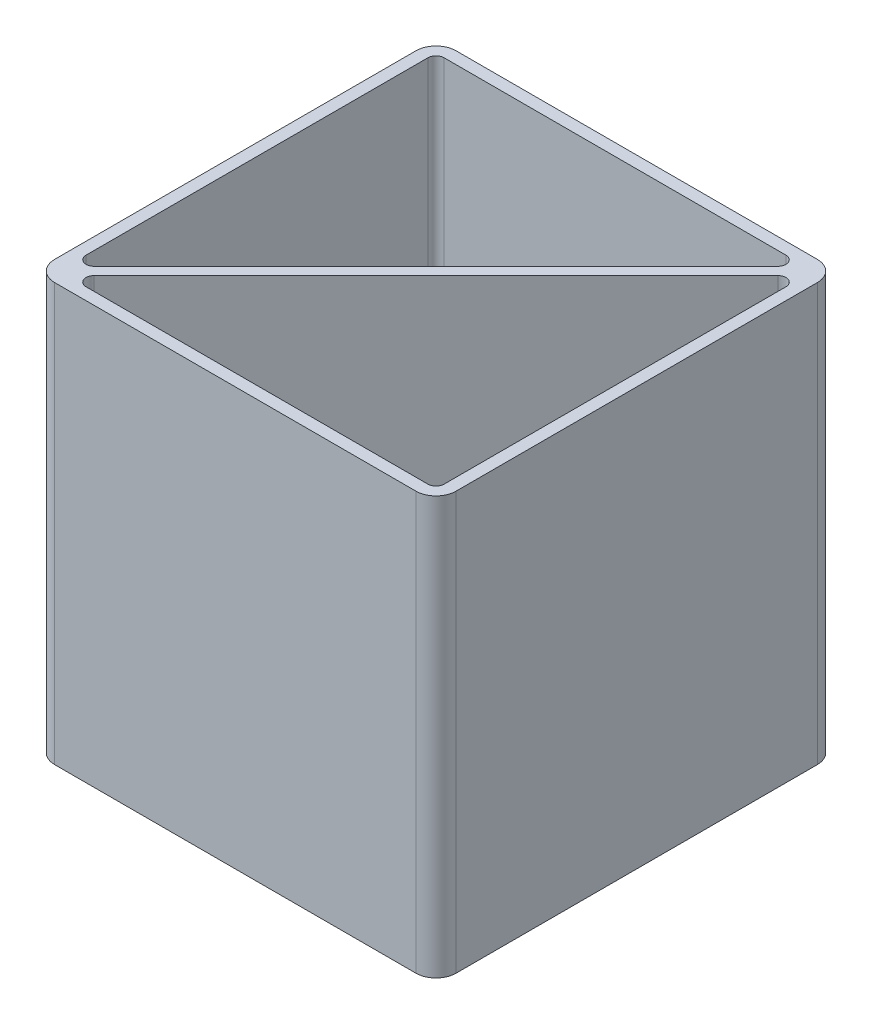
SolidWorks part; units mm, degrees
ref_plane "前视基准面" through (0, 0, 0) normal (0, 0, 1) x (1, 0, 0)
ref_plane "上视基准面" through (0, 0, 0) normal (0, 1, 0) x (1, 0, 0)
ref_plane "右视基准面" through (0, 0, 0) normal (1, 0, 0) x (0, 0, -1)
sketch "草图1" plane through (0, 0, 0) normal (0, 1, 0) x (1, 0, 0)
  line L1 (45, 50) -> (-45, 50)
  line L2 (-50, 45) -> (-50, -45)
  line L3 (-45, -50) -> (45, -50)
  line L4 (50, -45) -> (50, 45)
  line L5 (-29.6606, 50.0027) -> (-29.4089, 49.7457)
  line L6 (-29.4089, 49.7457) -> (-29.152, 49.9973)
  line L7 (-29.152, 49.9973) -> (-29.4036, 50.2543)
  line L8 (-29.4036, 50.2543) -> (-29.6606, 50.0027)
  circle A0 centre (0, 0) radius 50 construction
  circle A1 centre (-29.4063, 50) radius 0.1798 construction
  arc A2 (45, 50) -> (50, 45) centre (45, 45) cw
  arc A3 (50, -45) -> (45, -50) centre (45, -45) cw
  arc A4 (-50, -45) -> (-45, -50) centre (-45, -45) ccw
  arc A5 (-45, 50) -> (-50, 45) centre (-45, 45) ccw
  dimension "D2" = 5
  dimension "D1" = 50
extrude "凸台-拉伸1" add sketch "草图1" along normal blind 4 contours L1 A5 L2 A4 L3 A3 L4 A2 L7 L6 L5
ref_plane "基准面1" through (0, 4, 0) normal (0, 1, 0) x (1, 0, 0)
sketch "草图2" plane through (0, 4, 0) normal (0, 1, 0) x (1, 0, 0)
  line L0 (-47, 45) -> (-47, -40.1716)
  line L1 (45, 50) -> (-45, 50)
  line L2 (-50, 45) -> (-50, -45)
  line L3 (-45, -50) -> (45, -50)
  line L4 (50, -45) -> (50, 45)
  line L5 (-40.1716, -47) -> (45, -47)
  line L6 (47, -45) -> (47, 40.1716)
  line L7 (40.1716, 47) -> (-45, 47)
  line L8 (-43.5858, -41.5858) -> (41.5858, 43.5858)
  line L9 (43.5858, 41.5858) -> (-41.5858, -43.5858)
  line L10 (47, -45) -> (47, 45) construction
  line L11 (45, 47) -> (-45, 47) construction
  line L12 (-45, -47) -> (45, -47) construction
  line L13 (-47, 45) -> (-47, -45) construction
  circle A0 centre (0, 0) radius 50 construction
  arc A1 (50, 45) -> (45, 50) centre (45, 45) ccw
  arc A2 (50, -45) -> (45, -50) centre (45, -45) cw
  arc A3 (-45, -50) -> (-50, -45) centre (-45, -45) cw
  arc A4 (-45, 50) -> (-50, 45) centre (-45, 45) ccw
  arc A6 (47, -45) -> (45, -47) centre (45, -45) cw
  arc A8 (-45, 47) -> (-47, 45) centre (-45, 45) ccw
  arc A9 (-45, -47) -> (-47, -45) centre (-45, -45) cw construction
  arc A10 (47, 45) -> (45, 47) centre (45, 45) ccw construction
  arc A11 (43.5858, 41.5858) -> (47, 40.1716) centre (45, 40.1716) cw
  arc A12 (41.5858, 43.5858) -> (40.1716, 47) centre (40.1716, 45) ccw
  arc A13 (-40.1716, -47) -> (-41.5858, -43.5858) centre (-40.1716, -45) cw
  arc A14 (-43.5858, -41.5858) -> (-47, -40.1716) centre (-45, -40.1716) cw
  dimension "D2" = 5
  dimension "D5" = 2
  dimension "D1" = 50
  dimension "D3" = 3
extrude "凸台-拉伸3" add sketch "草图2" along normal blind 100
